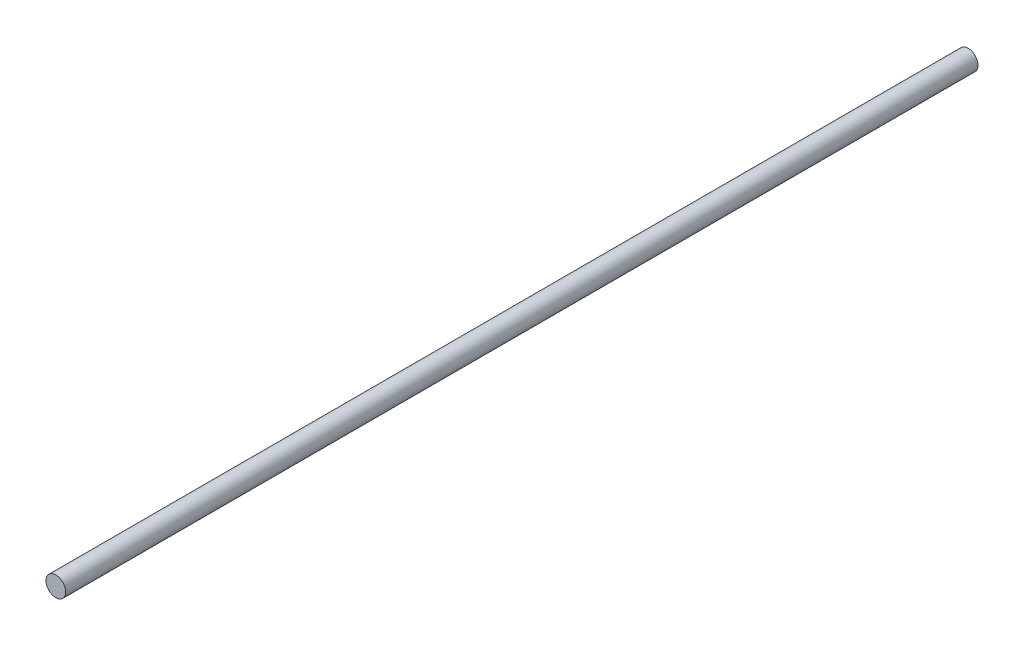
SolidWorks part; units mm, degrees
ref_plane "Front Plane" through (0, 0, 0) normal (0, 0, 1) x (1, 0, 0)
ref_plane "Top Plane" through (0, 0, 0) normal (0, 1, 0) x (1, 0, 0)
ref_plane "Right Plane" through (0, 0, 0) normal (1, 0, 0) x (0, 0, -1)
sketch "Sketch1" plane through (0, 0, 0) normal (0, 0, 1) x (1, 0, 0)
  circle A0 centre (0, 0) radius 4
  dimension "D1" = 8
extrude "Boss-Extrude1" add sketch "Sketch1" along normal blind 370
